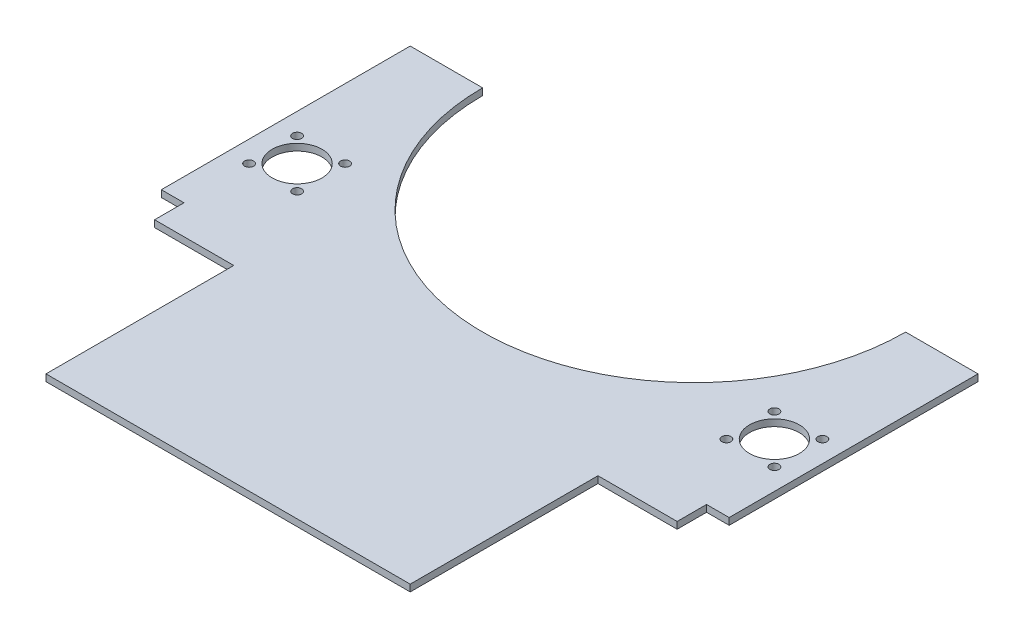
SolidWorks part; units mm, degrees
ref_plane "Face" through (0, 0, 0) normal (0, 0, 1) x (1, 0, 0)
ref_plane "Dessus" through (0, 0, 0) normal (0, 1, 0) x (1, 0, 0)
ref_plane "Droite" through (0, 0, 0) normal (1, 0, 0) x (0, 0, -1)
sketch "Esquisse1" plane through (0, 0, 0) normal (0, 1, 0) x (1, 0, 0)
  line L0 (0, 0) -> (0, 275.4932) construction
  line L1 (80.5, 0) -> (-80.5, 0)
  line L2 (-80.5, 0) -> (-80.5, 83)
  line L3 (-80.5, 83) -> (-115.5, 83)
  line L4 (-115.5, 83) -> (-115.5, 96)
  line L5 (-115.5, 96) -> (-125.5, 96)
  line L6 (-125.5, 96) -> (-125.5, 206)
  line L7 (-125.5, 206) -> (-93.5, 206)
  line L8 (-105.5, 206) -> (-105.5, 138.2422) construction
  line L9 (-125.5, 136) -> (-97.6476, 136) construction
  line L10 (125.5, 136) -> (97.6476, 136) construction
  line L11 (105.5, 206) -> (105.5, 138.2422) construction
  line L12 (125.5, 206) -> (93.5, 206)
  line L13 (125.5, 96) -> (125.5, 206)
  line L14 (115.5, 96) -> (125.5, 96)
  line L15 (115.5, 83) -> (115.5, 96)
  line L16 (80.5, 83) -> (115.5, 83)
  line L17 (80.5, 0) -> (80.5, 83)
  line L18 (-93.5, 206) -> (0, 206) construction
  circle A0 centre (94.89, 146.61) radius 2
  circle A1 centre (-105.5, 136) radius 11
  circle A2 centre (-116.11, 146.61) radius 2
  circle A3 centre (-116.11, 125.39) radius 2
  circle A4 centre (-94.89, 125.39) radius 2
  circle A5 centre (-94.89, 146.61) radius 2
  circle A6 centre (94.89, 125.39) radius 2
  circle A7 centre (116.11, 125.39) radius 2
  circle A8 centre (116.11, 146.61) radius 2
  circle A9 centre (105.5, 136) radius 11
  arc A10 (93.5, 206) -> (-93.5, 206) centre (0, 206) cw
  point P16 (-105.5, 136)
  dimension "D10" = 22
  dimension "D12" = 4
  dimension "D13" = 10.61
  dimension "D14" = 10.61
  dimension "D1" = 80.5
  dimension "D2" = 35
  dimension "D3" = 10
  dimension "D4" = 110
  dimension "D5" = 32
  dimension "D6" = 83
  dimension "D8" = 70
  dimension "D9" = 20
  dimension "D11" = 13
extrude "Extrusion1" add sketch "Esquisse1" along normal blind 3
